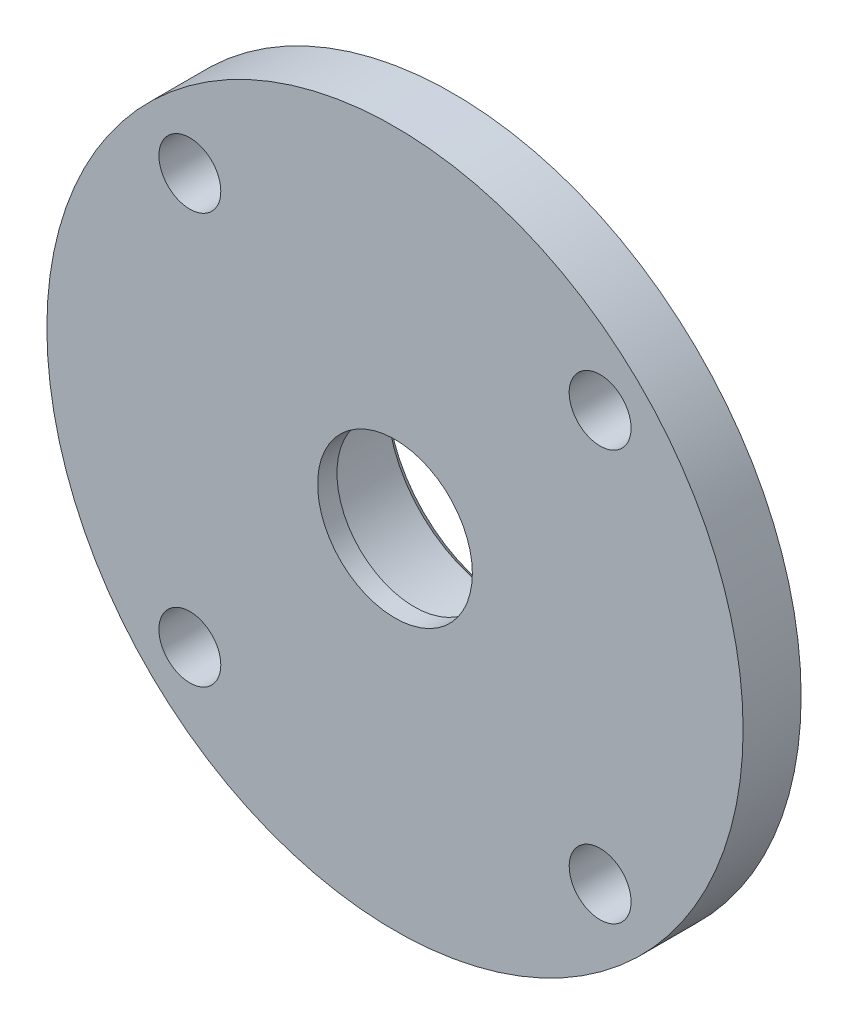
SolidWorks part; units mm, degrees
material "2024 Сплав"
ref_plane "Спереди" through (0, 0, 0) normal (0, 0, 1) x (1, 0, 0)
ref_plane "Сверху" through (0, 0, 0) normal (0, 1, 0) x (1, 0, 0)
ref_plane "Справа" through (0, 0, 0) normal (1, 0, 0) x (0, 0, -1)
sketch "Эскиз1" plane through (0, 0, 0) normal (0, 1, 0) x (1, 0, 0)
  line L0 (-4, 0) -> (-18, 0)
  line L1 (-18, 0) -> (-18, 3)
  line L2 (-18, 3) -> (-9.5, 3)
  line L3 (-9.5, 3) -> (-9.5, 6)
  line L8 (-9.5, 6) -> (-6, 6)
  line L9 (-6, 6) -> (-6, 1)
  line L10 (-6, 1) -> (-4, 1)
  line L11 (-4, 1) -> (-4, 0)
  line L12 (0, 0) -> (0, 50000) construction
  dimension "D1" = 4
  dimension "D2" = 18
  dimension "D3" = 9.5
  dimension "D6" = 1
  dimension "D7" = 6
  dimension "D8" = 6
  dimension "D9" = 3
revolve "Повернуть1" add sketch "Эскиз1" angle 360 about L12
sketch "Эскиз2" plane through (0, 0, 0) normal (0, 0, 1) x (1, 0, 0)
  line L0 (0, 0) -> (18, 0) construction
  circle A0 centre (10.6066, 10.6066) radius 1.6
  circle A1 centre (0, 0) radius 18 construction
  dimension "D2" = 3.2
  dimension "D1" = 45
  dimension "D3" = 15
extrude "Вырез-Вытянуть1" cut sketch "Эскиз2" against normal up to next (3 mm away)
pattern_circular "Круговой массив1" count 4 over 360 about axis through (0, 0, 0) along (0, 0, 1) of "Вырез-Вытянуть1"
chamfer "Фаска1" distance 0.4 angle 45 2 edges at (6, 0, -6) (9.5, 0, -6)
